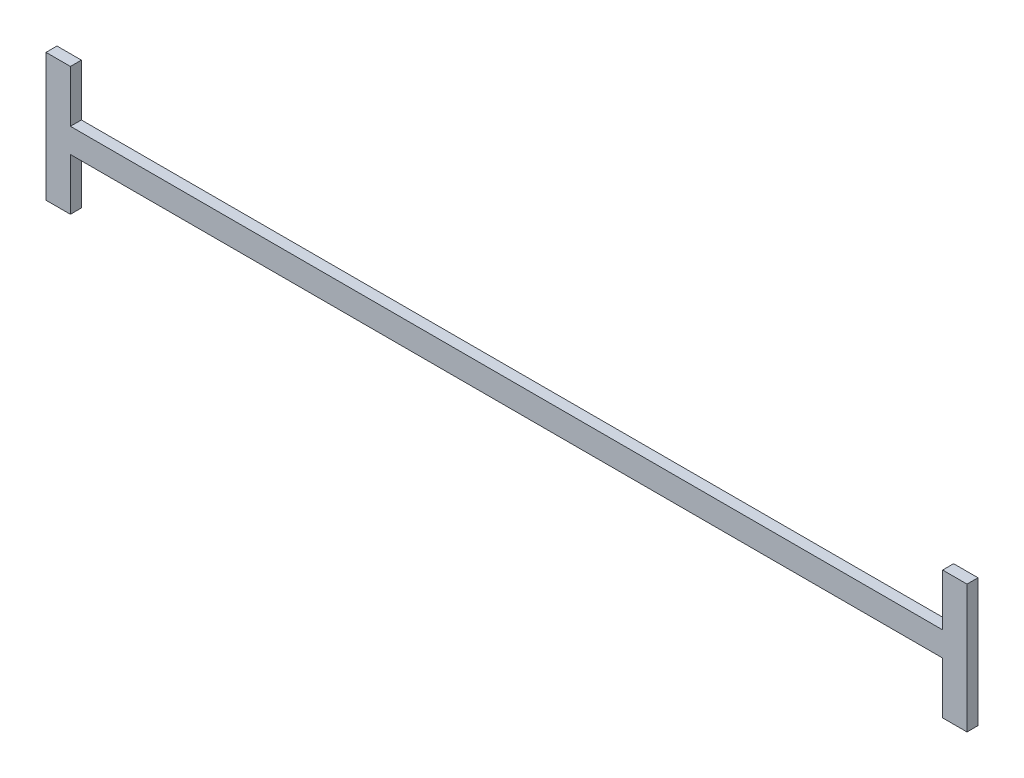
SolidWorks part; units mm, degrees
ref_plane "Alzado" through (0, 0, 0) normal (0, 0, 1) x (1, 0, 0)
ref_plane "Planta" through (0, 0, 0) normal (0, 1, 0) x (1, 0, 0)
ref_plane "Vista lateral" through (0, 0, 0) normal (1, 0, 0) x (0, 0, -1)
sketch "Croquis1" plane through (0, 0, 0) normal (0, 0, 1) x (1, 0, 0)
  line L0 (71.5, 0) -> (-71.5, 0)
  line L1 (-71.5, 0) -> (-71.5, -8.5)
  line L2 (-71.5, -8.5) -> (-75.5, -8.5)
  line L3 (-75.5, -8.5) -> (-75.5, 12.5)
  line L4 (-75.5, 12.5) -> (-71.5, 12.5)
  line L5 (-71.5, 12.5) -> (-71.5, 4)
  line L6 (-71.5, 4) -> (71.5, 4)
  line L7 (0, 4) -> (0, 0) construction
  line L8 (71.5, 12.5) -> (71.5, 4)
  line L9 (75.5, 12.5) -> (71.5, 12.5)
  line L10 (75.5, -8.5) -> (75.5, 12.5)
  line L11 (71.5, -8.5) -> (75.5, -8.5)
  line L12 (71.5, 0) -> (71.5, -8.5)
  dimension "D1" = 8.5
  dimension "D2" = 4
  dimension "D3" = 4
  dimension "D4" = 71.5
extrude "Saliente-Extruir1" add sketch "Croquis1" along normal blind 1.8
